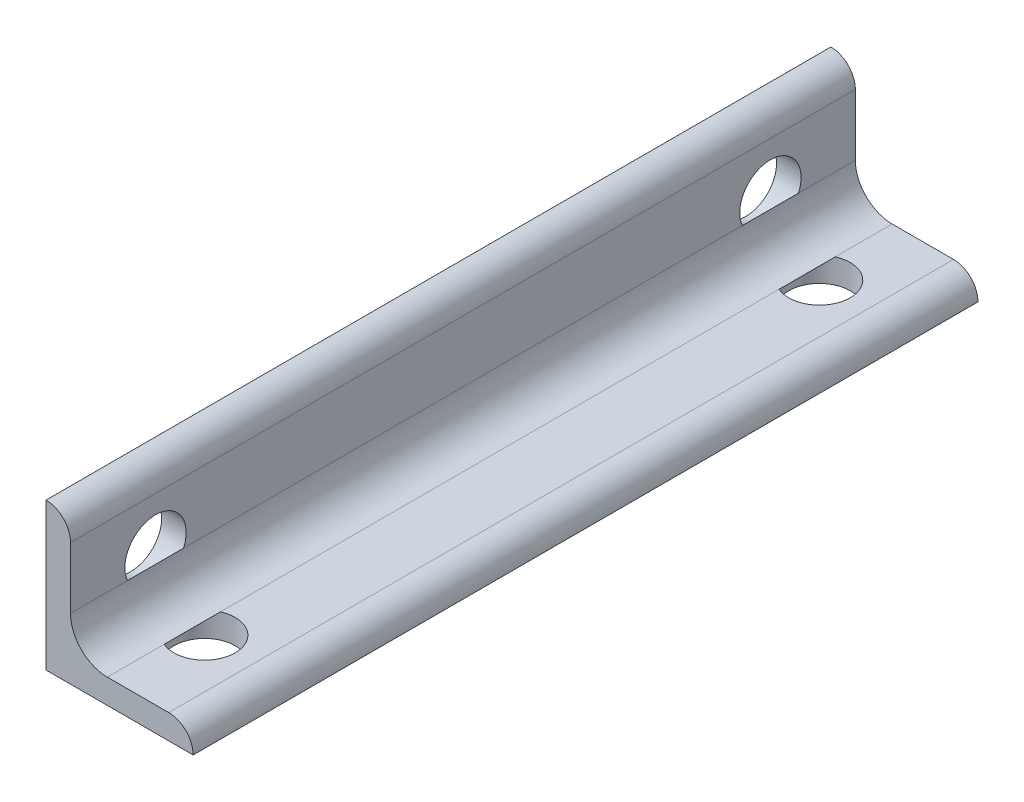
SolidWorks part; units mm, degrees
material "6063-T6"
ref_plane "Plane1" through (0, 0, 0) normal (0, 0, 1) x (1, 0, 0)
ref_plane "Plane2" through (0, 0, 0) normal (0, 1, 0) x (1, 0, 0)
ref_plane "Plane3" through (0, 0, 0) normal (1, 0, 0) x (0, 0, -1)
sketch "Sketch1" plane through (0, 0, 0) normal (0, 0, 1) x (1, 0, 0)
  line L0 (0, 0) -> (0, 19.05)
  line L1 (0, 19.05) -> (0.0051, 19.05)
  line L2 (3.175, 15.8801) -> (3.175, 7.9375)
  line L3 (7.9375, 3.175) -> (15.8801, 3.175)
  line L4 (19.05, 0.0051) -> (19.05, 0)
  line L5 (19.05, 0) -> (0, 0)
  arc A0 (19.05, 0.0051) -> (15.8801, 3.175) centre (15.8801, 0.0051) ccw
  arc A1 (0.0051, 19.05) -> (3.175, 15.8801) centre (0.0051, 15.8801) cw
  arc A2 (7.9375, 3.175) -> (3.175, 7.9375) centre (7.9375, 7.9375) cw
  circle A3 centre (0, 0) radius 3.175 construction
  dimension "D2" = 0.0051
  dimension "Radius_1" = 4.7625
  dimension "Radius_2" = 3.175
  dimension "D1" = 3.175
  dimension "V_leg" = 19.05
  dimension "H_leg" = 19.05
  dimension "Thickness" = 3.175
  dimension "Flat_wid" = 0.0051
extrude "BaseSteelAngle" add sketch "Sketch1" along normal mid plane 101.6
hole_wizard "5/16 (0.3125) Diameter Hole2" positions "Sketch5" profile "Sketch4" hole size "5/16" standard "Ansi Inch"
sketch "Sketch5" plane through (0, 3.175, 0) normal (0, 1, 0) x (-1, 0, 0)
  line L0 (-15.8801, 50.8) -> (-7.9375, 50.8) construction
  line L2 (-19.05, 50.8) -> (-19.05, -50.8) construction
  point P0 (-9.525, 39.8)
  dimension "D1" = 11
  dimension "D2" = 9.525
sketch "Sketch4" plane through (9.525, 3.175, 39.8) normal (1, 0, 0) x (0, 0, 1)
  line L0 (0, 0) -> (0, 21.4347)
  line L1 (0, 21.4347) -> (3.9687, 19.05)
  line L2 (3.9687, 19.05) -> (3.9687, 0)
  line L5 (3.9687, 0) -> (0, 0)
  line L10 (0, 21.4347) -> (-3.9687, 19.05) construction
  line L11 (0, -6.35) -> (0, 107.95) construction
  dimension "Hole Dia." = 7.9375
  dimension "Hole Depth" = 19.05
  dimension "Drill Angle" = 118
mirror "Mirror1" about plane through (0, 0, 0) normal (0, 0, 1) of "5/16 (0.3125) Diameter Hole2"
hole_wizard "5/16 (0.3125) Diameter Hole3" positions "Sketch7" profile "Sketch6" hole size "5/16" standard "Ansi Inch"
sketch "Sketch7" plane through (3.175, 0, 0) normal (1, 0, 0) x (0, 0, -1)
  line L0 (-50.8, 7.9375) -> (-50.8, 15.8801) construction
  line L2 (-50.8, 19.05) -> (50.8, 19.05) construction
  point P0 (-39.8, 9.525)
  dimension "D1" = 11
  dimension "D2" = 9.525
sketch "Sketch6" plane through (3.175, 9.525, 39.8) normal (0, 1, 0) x (0, 0, -1)
  line L0 (0, 0) -> (0, 21.4347)
  line L1 (0, 21.4347) -> (3.9687, 19.05)
  line L2 (3.9687, 19.05) -> (3.9687, 0)
  line L5 (3.9687, 0) -> (0, 0)
  line L10 (0, 21.4347) -> (-3.9687, 19.05) construction
  line L11 (0, -6.35) -> (0, 107.95) construction
  dimension "Hole Dia." = 7.9375
  dimension "Hole Depth" = 19.05
  dimension "Drill Angle" = 118
mirror "Mirror2" about plane through (0, 0, 0) normal (0, 0, 1) of "5/16 (0.3125) Diameter Hole3"
equation "\"Flat_wid@Sketch1\" = ((sgn(\"Thickness@Sketch1\" - \"Radius_2@Sketch1\") +1)*(\"Thickness@Sketch1\" - \"Radius_2@Sketch1\"))/2 +0.0002"
equation "\"D1@Sketch1\" = \"Thickness@Sketch1\""
equation "\"D2@Sketch1\" = \"Flat_wid@Sketch1\""
